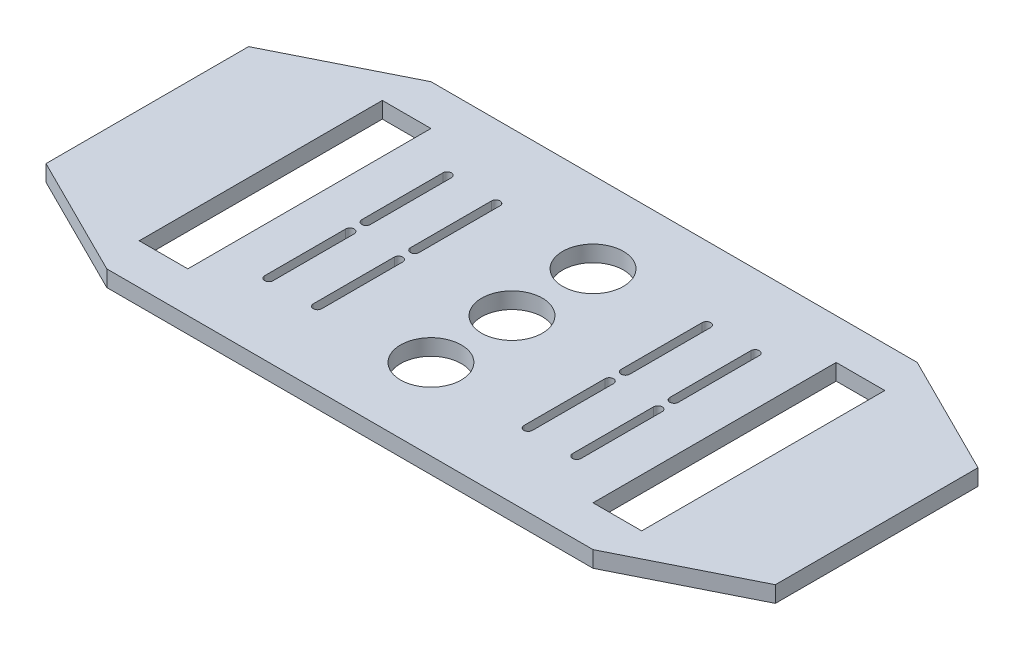
SolidWorks part; units mm, degrees
material "Pin"
ref_plane "Plan de face" through (0, 0, 0) normal (0, 0, 1) x (1, 0, 0)
ref_plane "Plan de dessus" through (0, 0, 0) normal (0, 1, 0) x (1, 0, 0)
ref_plane "Plan de droite" through (0, 0, 0) normal (1, 0, 0) x (0, 0, -1)
sketch "Esquisse1" plane through (0, 0, 0) normal (0, 1, 0) x (1, 0, 0)
  line L1 (0, 0) -> (180, 0)
  line L2 (0, 0) -> (0, 80)
  line L3 (0, 80) -> (180, 80)
  line L4 (180, 0) -> (180, 80)
  dimension "D1" = 80
  dimension "D2" = 180
extrude "Boss.-Extru.1" add sketch "Esquisse1" along normal blind 4
sketch "Esquisse2" plane through (0, 4, 0) normal (0, 1, 0) x (1, 0, 0)
  line L0 (30, 0) -> (0, 15)
  line L1 (0, 0) -> (180, 0) construction
  line L2 (0, 80) -> (0, 0) construction
  line L3 (0, 15) -> (0, 0)
  line L4 (0, 0) -> (30, 0)
  line L5 (30, 80) -> (0, 65)
  line L6 (180, 80) -> (0, 80) construction
  line L7 (0, 65) -> (0, 80)
  line L8 (0, 80) -> (30, 80)
  line L9 (150, 0) -> (180, 15)
  line L10 (180, 0) -> (180, 80) construction
  line L11 (180, 15) -> (180, 0)
  line L12 (180, 0) -> (150, 0)
  line L13 (150, 80) -> (180, 80)
  line L14 (180, 80) -> (180, 65)
  line L15 (180, 65) -> (150, 80)
  dimension "D1" = 15
  dimension "D2" = 30
  dimension "D3" = 30
  dimension "D4" = 15
  dimension "D5" = 15
  dimension "D6" = 30
  dimension "D7" = 30
  dimension "D8" = 15
extrude "Enlèv. mat.-Extru.1" cut sketch "Esquisse2" against normal blind 4
sketch "Esquisse3" plane through (0, 4, 0) normal (0, 1, 0) x (1, 0, 0)
  line L0 (8.5147, 40) -> (227.2024, 40) construction
  line L1 (30, 0) -> (150, 0) construction
  line L2 (90, 126.5747) -> (90, -53.3594) construction
  line L3 (150, 80) -> (30, 80) construction
  line L4 (0, 65) -> (0, 15) construction
  line L5 (64, 38) -> (64, 18) construction
  line L6 (65.05, 38) -> (65.05, 18)
  line L7 (62.95, 38) -> (62.95, 18)
  line L8 (52, 18) -> (52, 38) construction
  line L9 (50.95, 18) -> (50.95, 38)
  line L10 (53.05, 18) -> (53.05, 38)
  line L11 (128, 18) -> (128, 38) construction
  line L12 (129.05, 18) -> (129.05, 38)
  line L13 (126.95, 18) -> (126.95, 38)
  line L14 (116, 38) -> (116, 18) construction
  line L15 (114.95, 38) -> (114.95, 18)
  line L16 (117.05, 38) -> (117.05, 18)
  line L17 (52, 62) -> (52, 42) construction
  line L18 (50.95, 62) -> (50.95, 42)
  line L19 (53.05, 62) -> (53.05, 42)
  line L20 (64, 42) -> (64, 62) construction
  line L21 (65.05, 42) -> (65.05, 62)
  line L22 (62.95, 42) -> (62.95, 62)
  line L23 (116, 42) -> (116, 62) construction
  line L24 (114.95, 42) -> (114.95, 62)
  line L25 (117.05, 42) -> (117.05, 62)
  line L26 (128, 62) -> (128, 42) construction
  line L27 (129.05, 62) -> (129.05, 42)
  line L28 (126.95, 62) -> (126.95, 42)
  arc A0 (65.05, 38) -> (62.95, 38) centre (64, 38) ccw
  arc A1 (62.95, 18) -> (65.05, 18) centre (64, 18) ccw
  arc A2 (50.95, 18) -> (53.05, 18) centre (52, 18) ccw
  arc A3 (53.05, 38) -> (50.95, 38) centre (52, 38) ccw
  arc A4 (129.05, 18) -> (126.95, 18) centre (128, 18) cw
  arc A5 (126.95, 38) -> (129.05, 38) centre (128, 38) cw
  arc A6 (114.95, 38) -> (117.05, 38) centre (116, 38) cw
  arc A7 (117.05, 18) -> (114.95, 18) centre (116, 18) cw
  arc A8 (50.95, 62) -> (53.05, 62) centre (52, 62) cw
  arc A9 (53.05, 42) -> (50.95, 42) centre (52, 42) cw
  arc A10 (65.05, 42) -> (62.95, 42) centre (64, 42) cw
  arc A11 (62.95, 62) -> (65.05, 62) centre (64, 62) cw
  arc A12 (114.95, 42) -> (117.05, 42) centre (116, 42) ccw
  arc A13 (117.05, 62) -> (114.95, 62) centre (116, 62) ccw
  arc A14 (129.05, 62) -> (126.95, 62) centre (128, 62) ccw
  arc A15 (126.95, 42) -> (129.05, 42) centre (128, 42) ccw
  point P12 (64, 28)
  point P17 (52, 28)
  point P26 (128, 28)
  point P33 (116, 28)
  point P40 (52, 52)
  point P47 (64, 52)
  point P54 (116, 52)
  point P61 (128, 52)
  dimension "D1" = 40
  dimension "D2" = 90
  dimension "D3" = 20
  dimension "D4" = 20
  dimension "D5" = 2.1
  dimension "D6" = 2.1
  dimension "D7" = 12
  dimension "D8" = 12
  dimension "D9" = 12
  dimension "D10" = 26
extrude "Enlèv. mat.-Extru.2" cut sketch "Esquisse3" against normal blind 4
ref_plane "Plan8" through (90, 0, 0) normal (-1, 0, 0) x (0, 0, 1)
sketch "Esquisse11" plane through (0, 4, 0) normal (0, 1, 0) x (1, 0, 0)
  line L0 (0, 65) -> (0, 15) construction
  line L1 (28, 70) -> (40, 70)
  line L2 (28, 70) -> (28, 10)
  line L3 (28, 10) -> (40, 10)
  line L4 (40, 70) -> (40, 10)
  line L5 (30, 0) -> (150, 0) construction
  line L6 (150, 80) -> (30, 80) construction
  line L7 (90, 111.4033) -> (90, -12.0266) construction
  line L8 (152, 10) -> (140, 10)
  line L9 (140, 70) -> (140, 10)
  line L10 (152, 70) -> (140, 70)
  line L11 (152, 70) -> (152, 10)
  dimension "D1" = 12
  dimension "D2" = 28
  dimension "D3" = 10
  dimension "D4" = 10
  dimension "D5" = 90
extrude "Enlèv. mat.-Extru.5" cut sketch "Esquisse11" against normal up to next and the other way through all
sketch "Esquisse14" plane through (0, 4, 0) normal (0, 1, 0) x (1, 0, 0)
  line L0 (30, 0) -> (150, 0) construction
  line L1 (0, 65) -> (0, 15) construction
  circle A0 centre (90, 60) radius 7.5
  circle A1 centre (90, 40) radius 7.5
  circle A2 centre (90, 20) radius 7.5
  dimension "D1" = 15
  dimension "D2" = 15
  dimension "D3" = 15
  dimension "D4" = 40
  dimension "D5" = 20
  dimension "D6" = 20
  dimension "D7" = 90
extrude "Enlèv. mat.-Extru.6" cut sketch "Esquisse14" against normal up to next
equation "\"D8@Esquisse2\"=\"D1@Esquisse2\""
equation "\"D4@Esquisse2\"=\"D1@Esquisse2\""
equation "\"D5@Esquisse2\"=\"D1@Esquisse2\""
